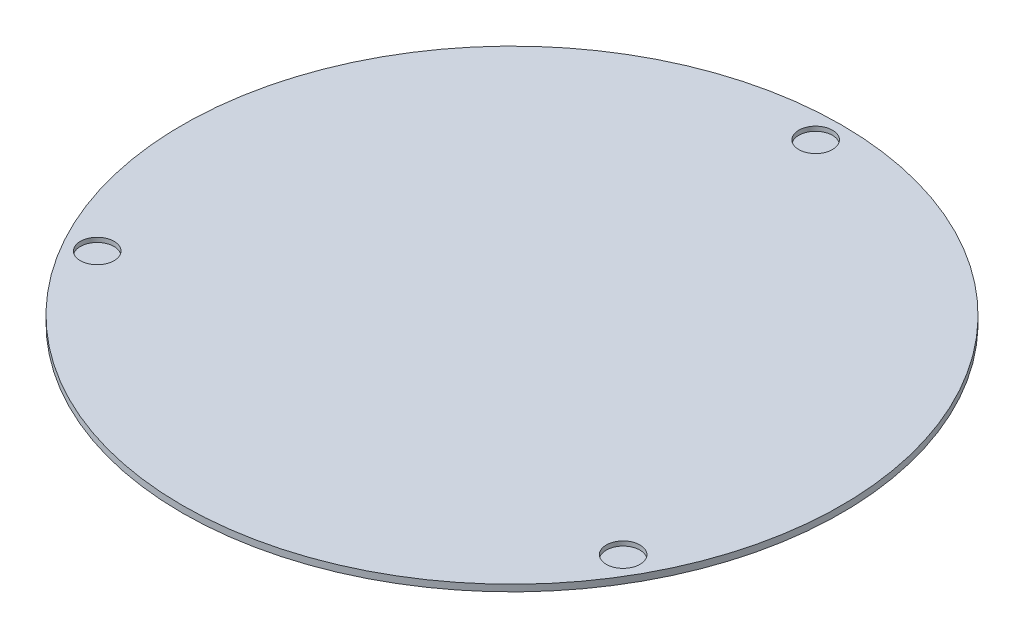
SolidWorks part; units mm, degrees
ref_plane "Front Plane" through (0, 0, 0) normal (0, 0, 1) x (1, 0, 0)
ref_plane "Top Plane" through (0, 0, 0) normal (0, 1, 0) x (1, 0, 0)
ref_plane "Right Plane" through (0, 0, 0) normal (1, 0, 0) x (0, 0, -1)
sketch "Sketch1" plane through (0, 0, 0) normal (0, 1, 0) x (1, 0, 0)
  circle A0 centre (0, 0) radius 149.225
  dimension "D1" = 298.45
extrude "Boss-Extrude1" add sketch "Sketch1" along normal blind 3
sketch "Sketch2" plane through (0, 3, 0) normal (0, 1, 0) x (1, 0, 0)
  line L0 (0, 0) -> (0, 160.2324) construction
  circle A0 centre (0, 137.4902) radius 7.62
  circle A1 centre (0, 0) radius 137.4902 construction
  circle A2 centre (119.07, -68.7451) radius 7.62
  circle A3 centre (-119.07, -68.7451) radius 7.62
  point P12 (0, 0)
  dimension "D1" = 274.9804
  dimension "D2" = 15.24
  dimension "D3" = 3
extrude "Cut-Extrude1" cut sketch "Sketch2" against normal blind 2.032
sketch "Sketch3" plane through (0, 3, 0) normal (0, 1, 0) x (1, 0, 0)
  line L0 (0, 16.1435) -> (0, -16.1435)
  line L1 (-16.1435, 0) -> (16.1435, 0)
  line L2 (-11.4152, 11.4152) -> (11.4152, -11.4152)
  line L3 (11.4152, 11.4152) -> (-11.4152, -11.4152)
  circle A0 centre (0, 0) radius 16.1435
  dimension "D1" = 45
